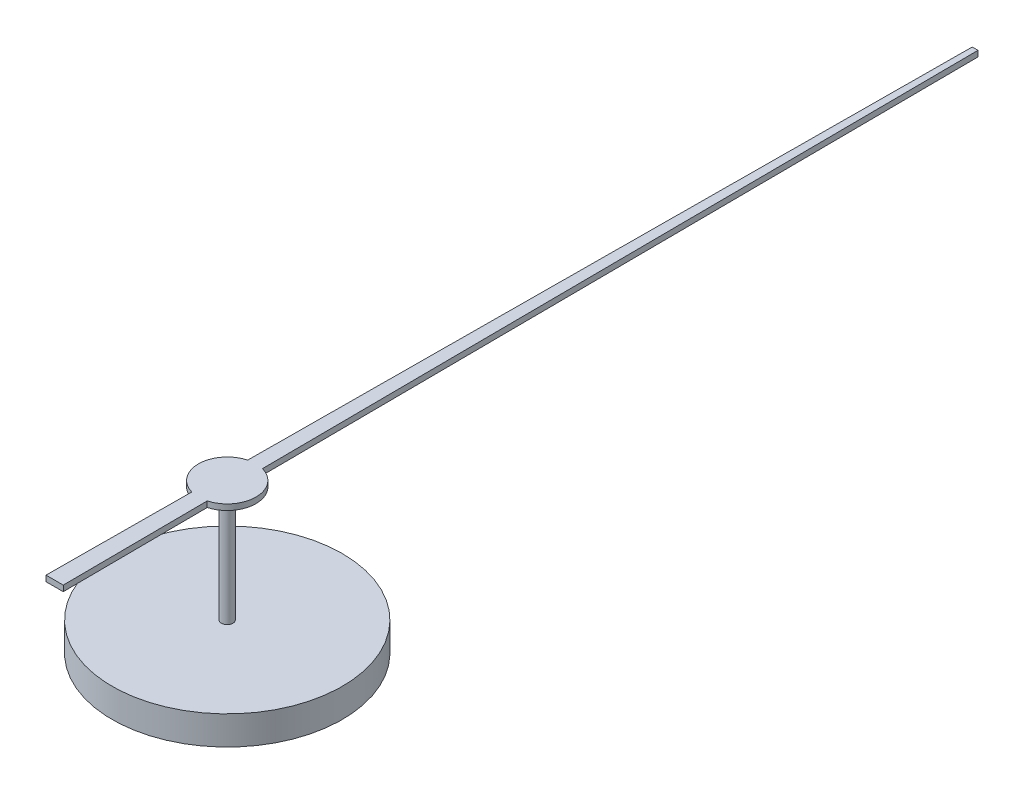
SolidWorks part; units mm, degrees
ref_plane "Front Plane" through (0, 0, 0) normal (0, 0, 1) x (1, 0, 0)
ref_plane "Top Plane" through (0, 0, 0) normal (0, 1, 0) x (1, 0, 0)
ref_plane "Right Plane" through (0, 0, 0) normal (1, 0, 0) x (0, 0, -1)
sketch "Sketch1" plane through (0, 0, 0) normal (0, 1, 0) x (1, 0, 0)
  line L0 (0, 71.7393) -> (0, -94.0328) construction
  line L1 (-2.0666, 0) -> (2.0487, 0) construction
  line L2 (-0.1282, 0.4833) -> (-0.05, 13)
  line L3 (0.15, -3) -> (-0.15, -3)
  line L4 (-0.15, -3) -> (-0.1343, -0.4816)
  line L5 (-0.05, 13) -> (0.05, 13)
  line L6 (0.15, -3) -> (0.1343, -0.4816)
  line L7 (0.1282, 0.4833) -> (0.05, 13)
  arc A0 (0.1343, -0.4816) -> (0.1282, 0.4833) centre (0, 0) ccw
  arc A1 (-0.1282, 0.4833) -> (-0.1343, -0.4816) centre (0, 0) ccw
  point P13 (0, 13)
  dimension "D2" = 16
  dimension "D4" = 0.05
extrude "Boss-Extrude1" add sketch "Sketch1" along normal blind 0.1
sketch "Sketch2" plane through (0, 0, 0) normal (0, -1, 0) x (1, 0, 0)
  circle A0 centre (0, 0) radius 0.1
  dimension "D1" = 0.2
extrude "Boss-Extrude2" add sketch "Sketch2" along normal blind 2
sketch "Sketch3" plane through (0, -2, 0) normal (0, -1, 0) x (1, 0, 0)
  circle A0 centre (0, 0) radius 2
  dimension "D1" = 4
extrude "Boss-Extrude3" add sketch "Sketch3" along normal blind 0.5
